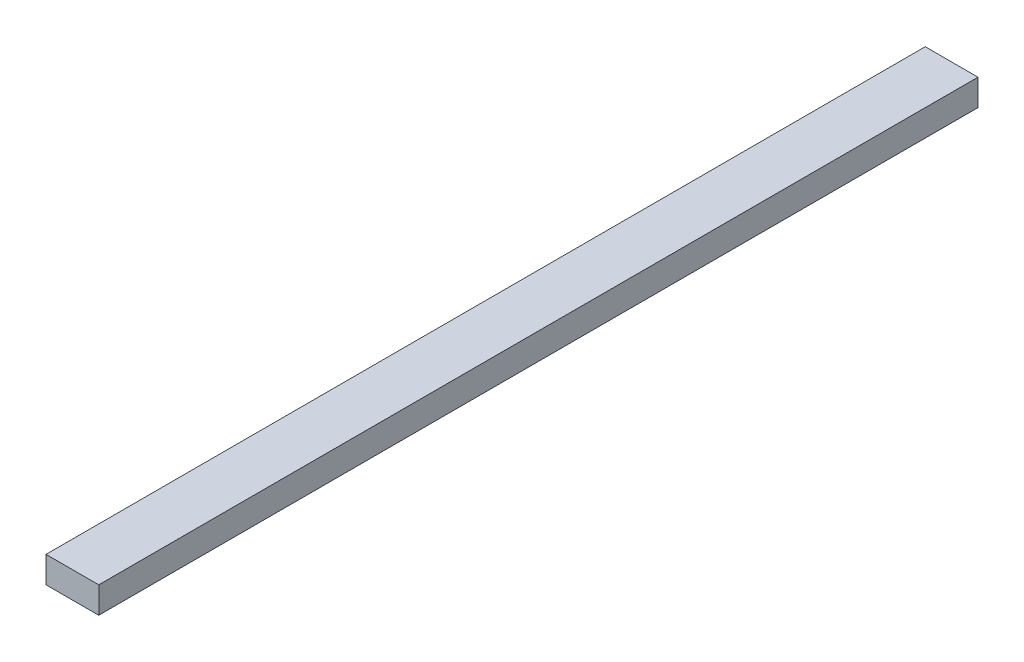
SolidWorks part; units mm, degrees
ref_plane "Front Plane" through (0, 0, 0) normal (0, 0, 1) x (1, 0, 0)
ref_plane "Top Plane" through (0, 0, 0) normal (0, 1, 0) x (1, 0, 0)
ref_plane "Right Plane" through (0, 0, 0) normal (1, 0, 0) x (0, 0, -1)
sketch "Sketch1" plane through (0, 0, 0) normal (0, 0, 1) x (1, 0, 0)
  line L1 (-9.4842, -4.6459) -> (20.5158, -4.6459)
  line L2 (-9.4842, -4.6459) -> (-9.4842, -19.6459)
  line L3 (-9.4842, -19.6459) -> (20.5158, -19.6459)
  line L4 (20.5158, -4.6459) -> (20.5158, -19.6459)
extrude "Boss-Extrude1" add sketch "Sketch1" along normal blind 500
